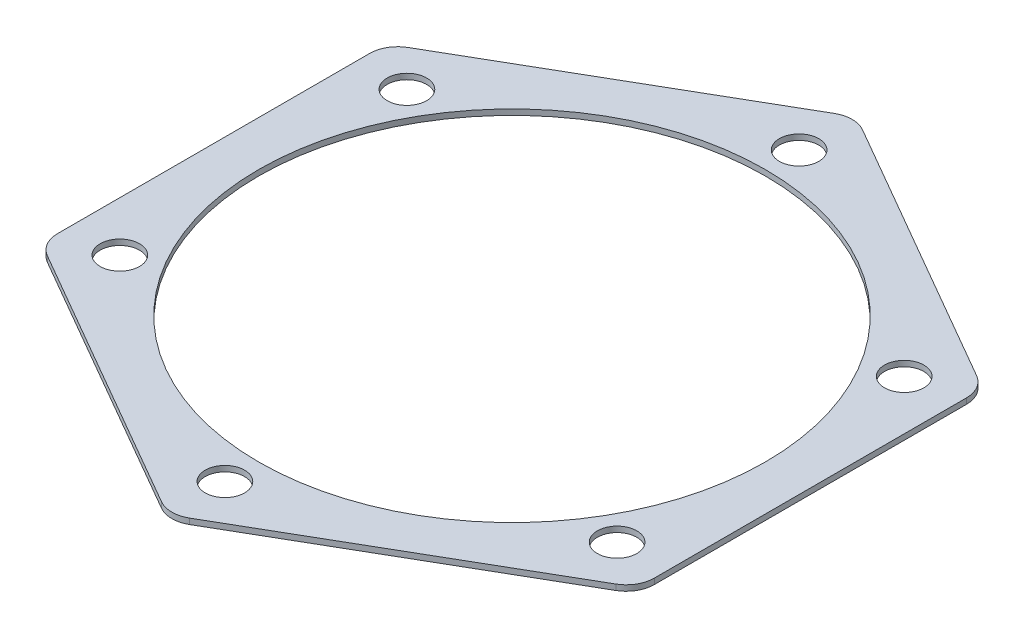
SolidWorks part; units mm, degrees
ref_plane "Front Plane" through (0, 0, 0) normal (0, 0, 1) x (1, 0, 0)
ref_plane "Top Plane" through (0, 0, 0) normal (0, 1, 0) x (1, 0, 0)
ref_plane "Right Plane" through (0, 0, 0) normal (1, 0, 0) x (0, 0, -1)
sketch "Sketch1" plane through (0, 0, 0) normal (0, 1, 0) x (1, 0, 0)
  line L1 (-2.5, 59.7558) -> (-50.5, 32.0429)
  line L2 (-53, 27.7128) -> (-53, -27.7128)
  line L3 (-50.5, -32.0429) -> (-2.5, -59.7558)
  line L4 (2.5, -59.7558) -> (50.5, -32.0429)
  line L5 (53, -27.7128) -> (53, 27.7128)
  line L6 (50.5, 32.0429) -> (2.5, 59.7558)
  circle A0 centre (0, 0) radius 53 construction
  circle A1 centre (0, 0) radius 51 construction
  circle A2 centre (0, 0) radius 45
  circle A3 centre (0, 51) radius 3.5
  circle A4 centre (44.1673, 25.5) radius 3.5
  circle A5 centre (44.1673, -25.5) radius 3.5
  circle A6 centre (0, -51) radius 3.5
  circle A7 centre (-44.1673, -25.5) radius 3.5
  circle A8 centre (-44.1673, 25.5) radius 3.5
  arc A9 (-53, -27.7128) -> (-50.5, -32.0429) centre (-48, -27.7128) ccw
  arc A10 (-2.5, -59.7558) -> (2.5, -59.7558) centre (0, -55.4256) ccw
  arc A11 (50.5, -32.0429) -> (53, -27.7128) centre (48, -27.7128) ccw
  arc A12 (53, 27.7128) -> (50.5, 32.0429) centre (48, 27.7128) ccw
  arc A13 (-2.5, 59.7558) -> (2.5, 59.7558) centre (0, 55.4256) cw
  arc A14 (-50.5, 32.0429) -> (-53, 27.7128) centre (-48, 27.7128) ccw
  point P33 (0, 61.1991)
  dimension "D2" = 102
  dimension "D3" = 90
  dimension "D4" = 7
  dimension "D6" = 5
  dimension "D1" = 106
  dimension "D5" = 6
extrude "Boss-Extrude1" add sketch "Sketch1" along normal blind 1
